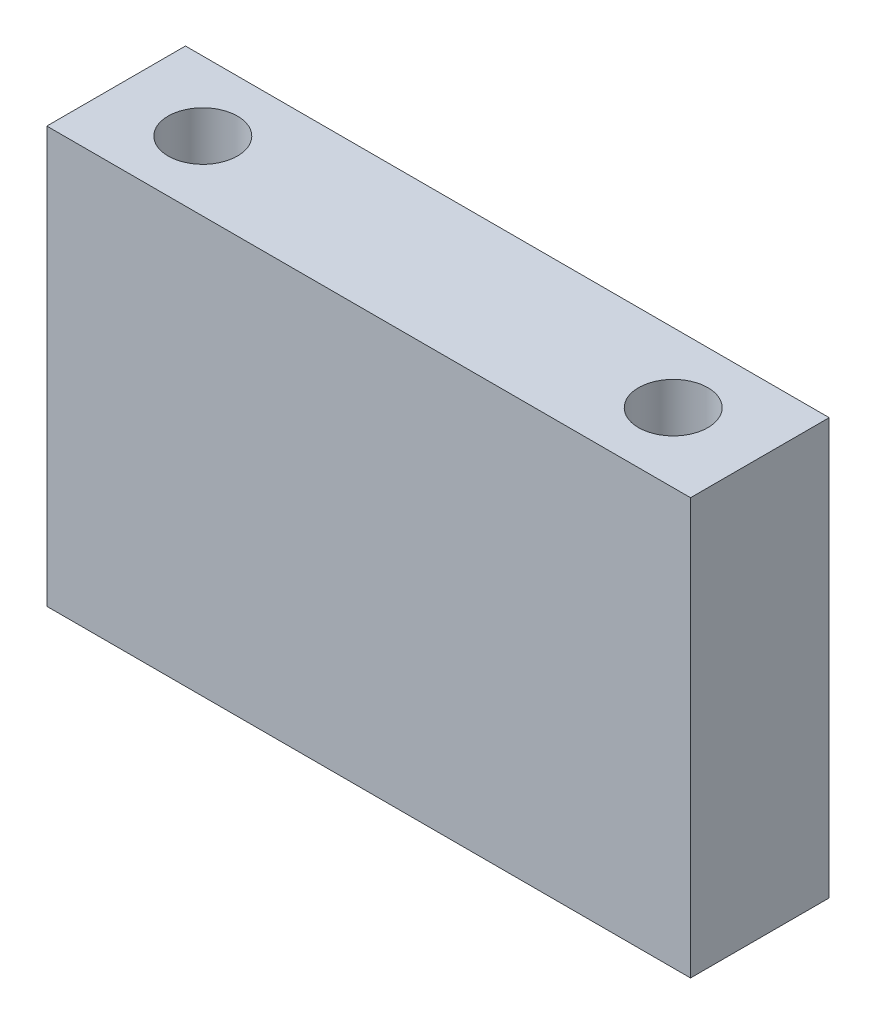
SolidWorks part; units mm, degrees
ref_plane "Plan de face" through (0, 0, 0) normal (0, 0, 1) x (1, 0, 0)
ref_plane "Plan de dessus" through (0, 0, 0) normal (0, 1, 0) x (1, 0, 0)
ref_plane "Plan de droite" through (0, 0, 0) normal (1, 0, 0) x (0, 0, -1)
sketch "Sketch1" plane through (0, 0, 0) normal (0, 0, 1) x (1, 0, 0)
  line L1 (0, 0) -> (65, 0)
  line L2 (0, 0) -> (0, 42)
  line L3 (0, 42) -> (65, 42)
  line L4 (65, 0) -> (65, 42)
  dimension "D1" = 65
  dimension "D2" = 42
extrude "Extrude1" add sketch "Sketch1" along normal blind 14
sketch "Sketch2" plane through (0, 42, 0) normal (0, 1, 0) x (1, 0, 0)
  line L0 (0, -7) -> (65, -7) construction
  line L1 (0, -14) -> (0, 0) construction
  line L2 (65, -14) -> (65, 0) construction
  line L3 (32.5, 0) -> (32.5, -14) construction
  line L4 (65, 0) -> (0, 0) construction
  line L5 (65, -14) -> (0, -14) construction
  circle A0 centre (8.75, -7) radius 3.5
  circle A1 centre (56.25, -7) radius 3.5
  point P16 (0, 0)
  dimension "D1" = 7
  dimension "D2" = 47.5
extrude "Extrude2" cut sketch "Sketch2" against normal through all
